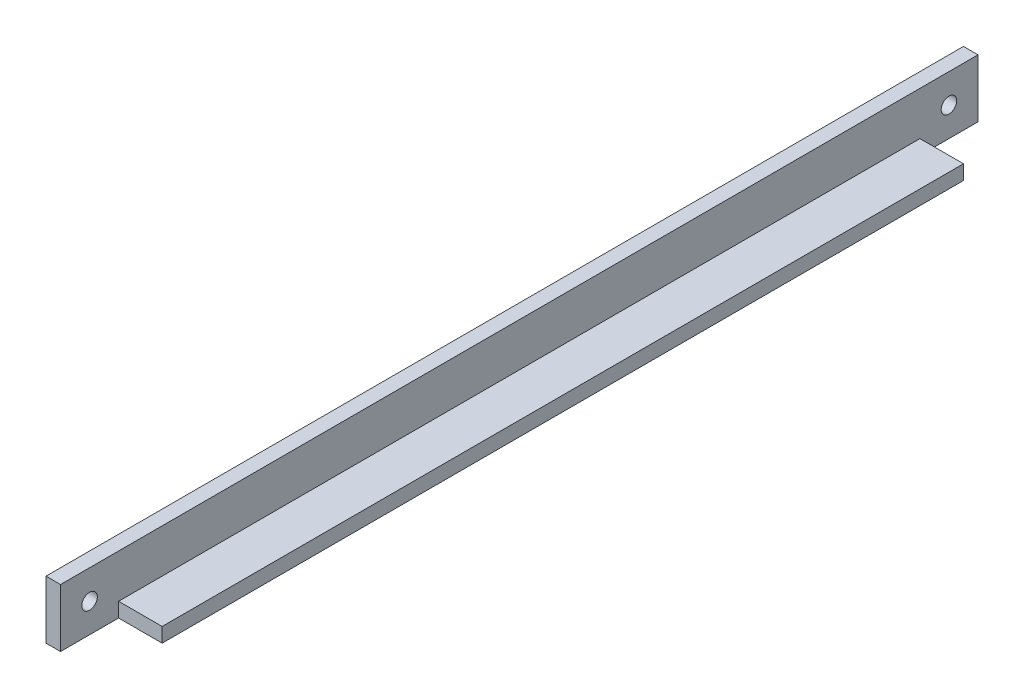
SolidWorks part; units mm, degrees
material "6061 Alloy"
ref_plane "Front Plane" through (0, 0, 0) normal (0, 0, 1) x (1, 0, 0)
ref_plane "Top Plane" through (0, 0, 0) normal (0, 1, 0) x (1, 0, 0)
ref_plane "Right Plane" through (0, 0, 0) normal (1, 0, 0) x (0, 0, -1)
sketch "Sketch1" plane through (0, 0, 0) normal (0, 0, 1) x (1, 0, 0)
  line L0 (0, 0) -> (0, 12.7)
  line L1 (0, 12.7) -> (3.175, 12.7)
  line L2 (3.175, 12.7) -> (3.175, 3.175)
  line L3 (3.175, 3.175) -> (12.7, 3.175)
  line L4 (12.7, 3.175) -> (12.7, 0)
  line L5 (12.7, 0) -> (0, 0)
  dimension "D1" = 12.7
  dimension "D2" = 12.7
  dimension "D3" = 3.175
  dimension "D4" = 3.175
extrude "Boss-Extrude1" add sketch "Sketch1" along normal blind 200.66
sketch "Sketch2" plane through (0, 3.175, 0) normal (0, 1, 0) x (1, 0, 0)
  line L0 (3.175, -200.66) -> (3.175, 0) construction
  line L1 (12.7, 0) -> (3.175, 0)
  line L2 (12.7, 0) -> (12.7, -12.7)
  line L3 (12.7, -12.7) -> (3.175, -12.7)
  line L4 (3.175, 0) -> (3.175, -12.7)
  line L5 (12.7, -200.66) -> (12.7, 0) construction
  line L6 (3.175, -200.66) -> (12.7, -200.66)
  line L7 (3.175, -200.66) -> (3.175, -187.96)
  line L8 (3.175, -187.96) -> (12.7, -187.96)
  line L9 (12.7, -200.66) -> (12.7, -187.96)
  dimension "D1" = 175.26
extrude "Cut-Extrude1" cut sketch "Sketch2" against normal through all
sketch "Sketch4" plane through (0, 0, 0) normal (-1, 0, 0) x (0, 0, 1)
  line L0 (0, 6.35) -> (200.66, 6.35) construction
  line L1 (0, 12.7) -> (0, 0) construction
  line L2 (200.66, 12.7) -> (200.66, 0) construction
  line L3 (194.31, 12.7) -> (194.31, 0) construction
  line L4 (200.66, 12.7) -> (0, 12.7) construction
  line L5 (200.66, 0) -> (0, 0) construction
  line L6 (6.35, 12.7) -> (6.35, 0) construction
  dimension "D1" = 6.35
  dimension "D2" = 6.35
hole_wizard "M3 Clearance Hole1" positions "3DSketch2" profile "Sketch5" hole size "M3" standard "ANSI Metric" end condition through all
sketch3d "3DSketch2"
  line L0 (0, 12.7, 6.35) -> (0, 0, 6.35) construction
  line L1 (0, 12.7, 194.31) -> (0, 0, 194.31) construction
  point P0 (0, 6.35, 6.35)
  point P5 (0, 6.35, 194.31)
  point P10 (0, 0, 0)
sketch "Sketch5" plane through (0, 6.35, 6.35) normal (0, 1, 0) x (0, 0, 1)
  line L0 (0, 0) -> (0, 12.7)
  line L1 (0, 12.7) -> (1.7, 12.7)
  line L2 (1.7, 12.7) -> (1.7, 0)
  line L5 (1.7, 0) -> (0, 0)
  line L11 (0, -6.35) -> (0, 107.95) construction
  dimension "Thru Hole Dia." = 3.4
  dimension "Thru Hole Depth" = 12.7
equation "\"D2@Sketch1\"=\"D1@Sketch1\""
equation "\"D4@Sketch1\"=\"D3@Sketch1\""
equation "\"D2@Sketch4\"=\"D1@Sketch4\""
